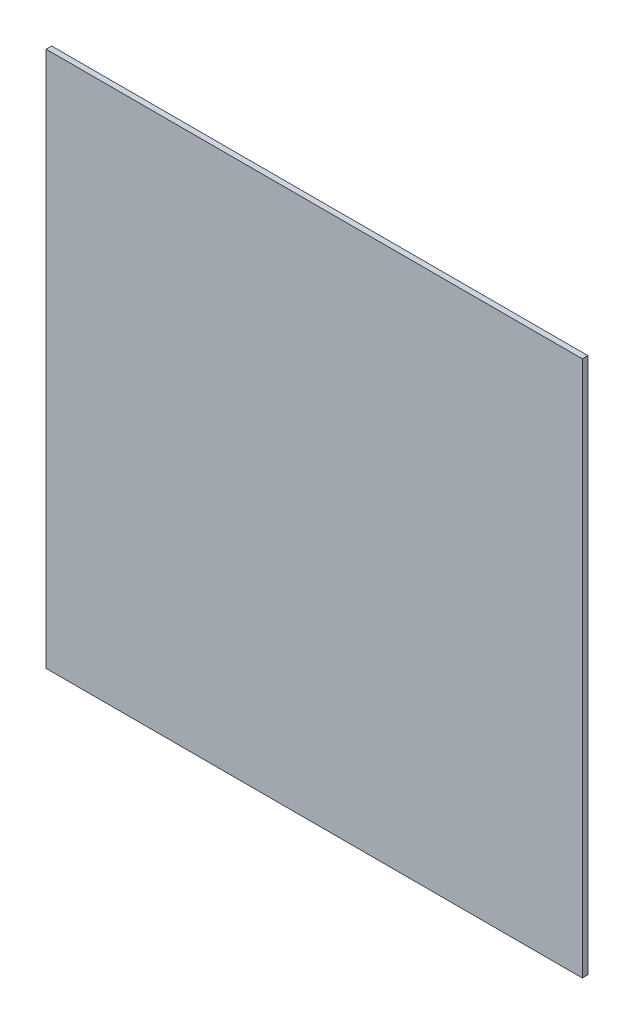
SolidWorks part; units mm, degrees
ref_plane "Front Plane" through (0, 0, 0) normal (0, 0, 1) x (1, 0, 0)
ref_plane "Top Plane" through (0, 0, 0) normal (0, 1, 0) x (1, 0, 0)
ref_plane "Right Plane" through (0, 0, 0) normal (1, 0, 0) x (0, 0, -1)
sketch "Sketch1" plane through (0, 0, 0) normal (0, 0, 1) x (1, 0, 0)
  line L1 (-152.4, -152.4) -> (152.4, -152.4)
  line L2 (-152.4, -152.4) -> (-152.4, 152.4)
  line L3 (-152.4, 152.4) -> (152.4, 152.4)
  line L4 (152.4, -152.4) -> (152.4, 152.4)
  line L5 (-152.4, -152.4) -> (152.4, 152.4) construction
  line L6 (-152.4, 152.4) -> (152.4, -152.4) construction
  point P0 (0, 0)
  dimension "D1" = 304.8
  dimension "D2" = 304.8
extrude "Boss-Extrude1" add sketch "Sketch1" along normal blind 3.175
